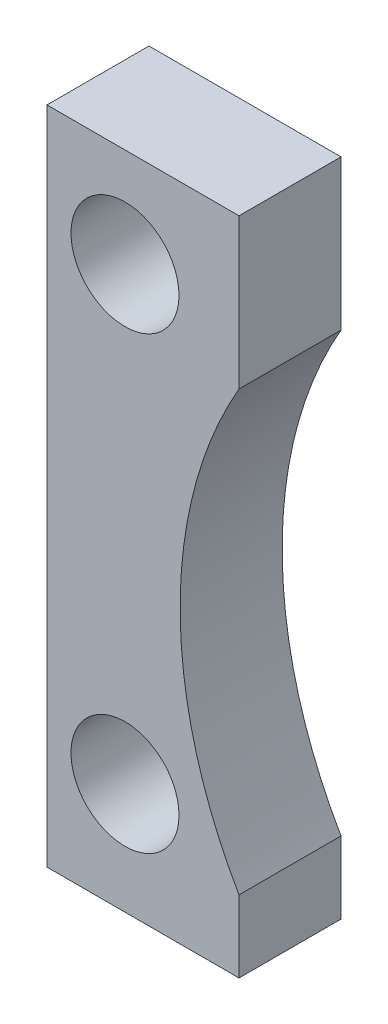
SolidWorks part; units mm, degrees
ref_plane "Front Plane" through (0, 0, 0) normal (0, 0, 1) x (1, 0, 0)
ref_plane "Top Plane" through (0, 0, 0) normal (0, 1, 0) x (1, 0, 0)
ref_plane "Right Plane" through (0, 0, 0) normal (1, 0, 0) x (0, 0, -1)
sketch "Çizim1" plane through (0, 0, 0) normal (0, 0, 1) x (1, 0, 0)
  line L0 (0, 0) -> (0, 110)
  line L1 (0, 110) -> (32, 110)
  line L2 (32, 110) -> (32, 85)
  line L3 (0, 0) -> (32, 0)
  line L4 (32, 0) -> (32, 12)
  arc A0 (32, 12) -> (32, 85) centre (95, 48.5) cw
  dimension "D1" = 110
  dimension "D2" = 32
  dimension "D3" = 25
  dimension "D4" = 12
  dimension "D5" = 95
extrude "Yükseklik-Ekstrüzyon1" add sketch "Çizim1" along normal mid plane 17
sketch "Çizim2" plane through (0, 0, 8.5) normal (0, 0, 1) x (1, 0, 0)
  circle A0 centre (13, 93.5) radius 9
  circle A1 centre (13, 18.5) radius 9
  dimension "D1" = 18
extrude "Kes-Ekstrüzyon1" cut sketch "Çizim2" against normal through all
